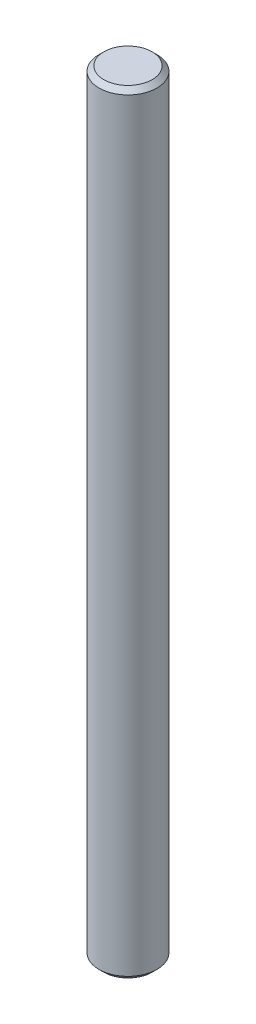
SolidWorks part; units mm, degrees
ref_plane "Front Plane" through (0, 0, 0) normal (0, 0, 1) x (1, 0, 0)
ref_plane "Top Plane" through (0, 0, 0) normal (0, 1, 0) x (1, 0, 0)
ref_plane "Right Plane" through (0, 0, 0) normal (1, 0, 0) x (0, 0, -1)
sketch "Sketch1" plane through (0, 0, 0) normal (0, 1, 0) x (1, 0, 0)
  circle A0 centre (0, 0) radius 3
  dimension "D1" = 6
extrude "Boss-Extrude1" add sketch "Sketch1" along normal blind 80
chamfer "Chamfer1" distance 0.5 angle 45 2 edges at (0, 0, 3) (0, 80, 3)
